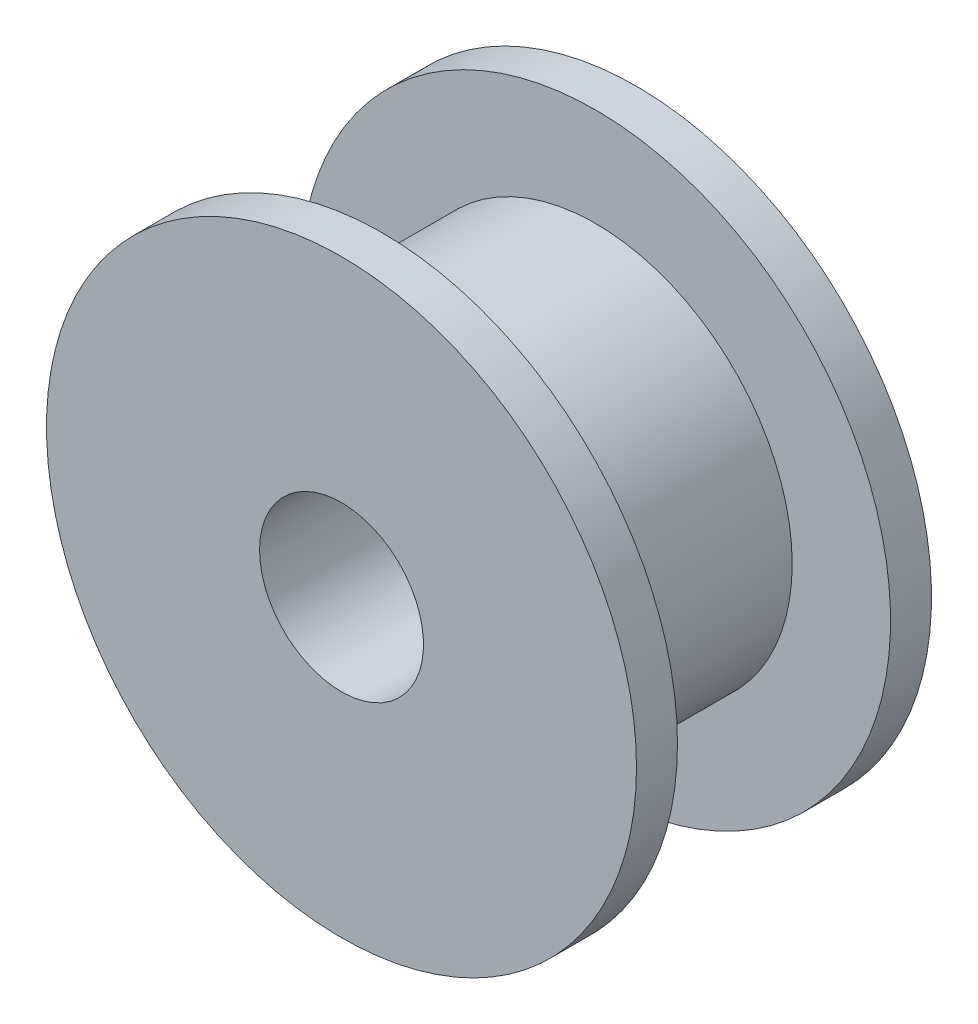
SolidWorks part; units mm, degrees
ref_plane "Alzado" through (0, 0, 0) normal (0, 0, 1) x (1, 0, 0)
ref_plane "Planta" through (0, 0, 0) normal (0, 1, 0) x (1, 0, 0)
ref_plane "Vista lateral" through (0, 0, 0) normal (1, 0, 0) x (0, 0, -1)
sketch "Croquis1" plane through (0, 0, 0) normal (0, 0, 1) x (1, 0, 0)
  circle A0 centre (0, 0) radius 6
  dimension "D1" = 12
extrude "Saliente-Extruir1" add sketch "Croquis1" along normal blind 6.5
sketch "Croquis2" plane through (0, 0, 6.5) normal (0, 0, 1) x (1, 0, 0)
  circle A0 centre (0, 0) radius 9
  dimension "D1" = 18
extrude "Saliente-Extruir2" add sketch "Croquis2" along normal blind 1.25
sketch "Croquis3" plane through (0, 0, 0) normal (0, 0, -1) x (-1, 0, 0)
  circle A0 centre (0, 0) radius 9
  dimension "D1" = 18
extrude "Saliente-Extruir3" add sketch "Croquis3" along normal blind 1.25
sketch "Croquis4" plane through (0, 0, -1.25) normal (0, 0, -1) x (-1, 0, 0)
  circle A0 centre (0, 0) radius 2.5
  circle A1 centre (0, 0) radius 9 construction
  dimension "D1" = 5
extrude "Cortar-Extruir1" cut sketch "Croquis4" against normal through all
